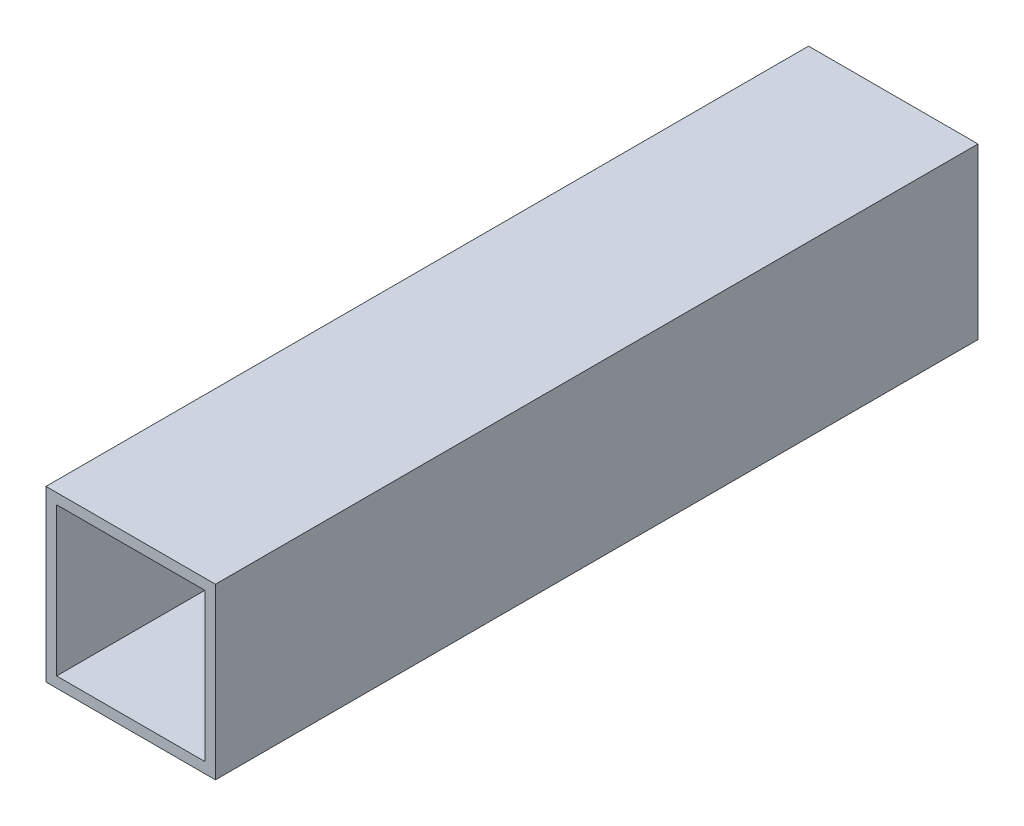
SolidWorks part; units mm, degrees
material "6061-T6 (SS)"
ref_plane "Front Plane" through (0, 0, 0) normal (0, 0, 1) x (1, 0, 0)
ref_plane "Top Plane" through (0, 0, 0) normal (0, 1, 0) x (1, 0, 0)
ref_plane "Right Plane" through (0, 0, 0) normal (1, 0, 0) x (0, 0, -1)
sketch "Sketch1" plane through (0, 0, 0) normal (0, 0, 1) x (1, 0, 0)
  line L0 (3.175, 47.625) -> (47.625, 47.625)
  line L1 (0, 0) -> (50.8, 0)
  line L2 (0, 0) -> (0, 50.8)
  line L3 (0, 50.8) -> (50.8, 50.8)
  line L4 (50.8, 0) -> (50.8, 50.8)
  line L5 (47.625, 3.175) -> (47.625, 47.625)
  line L6 (3.175, 3.175) -> (47.625, 3.175)
  line L7 (3.175, 3.175) -> (3.175, 47.625)
  dimension "D1" = 50.8
  dimension "D2" = 50.8
  dimension "D3" = 3.175
extrude "Boss-Extrude1" add sketch "Sketch1" along normal blind 228.6
